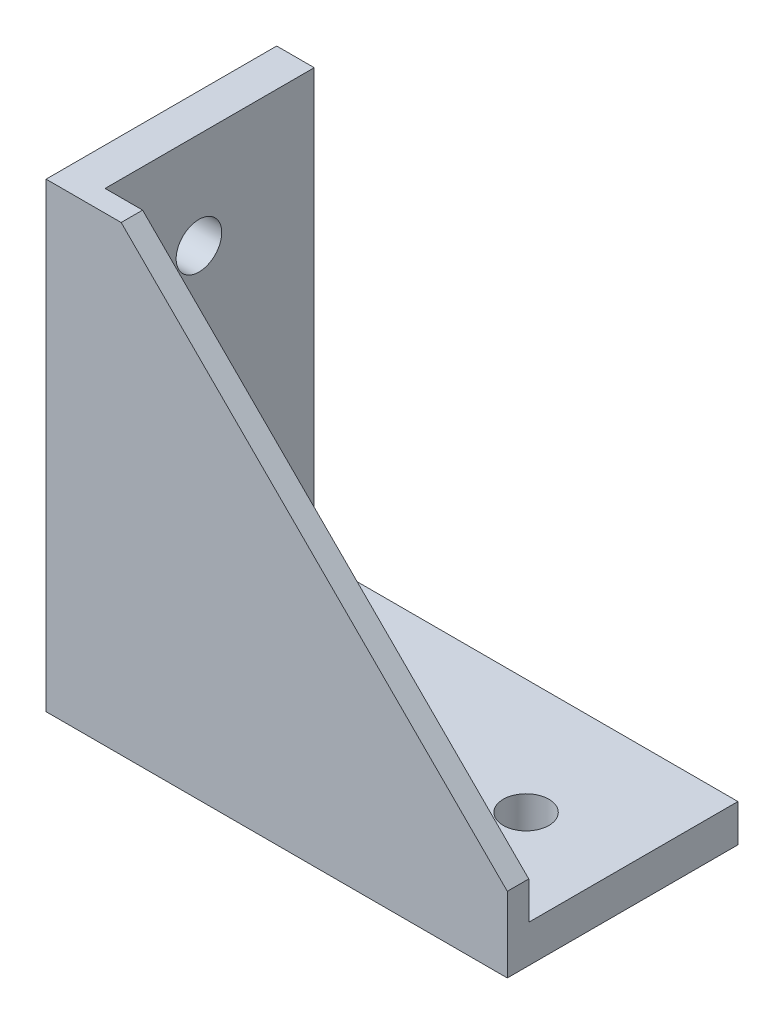
SolidWorks part; units mm, degrees
material "Алюминиевый сплав"
ref_plane "Спереди" through (0, 0, 0) normal (0, 0, 1) x (1, 0, 0)
ref_plane "Сверху" through (0, 0, 0) normal (0, 1, 0) x (1, 0, 0)
ref_plane "Справа" through (0, 0, 0) normal (1, 0, 0) x (0, 0, -1)
sketch "Эскиз1" plane through (0, 0, 0) normal (0, 0, 1) x (1, 0, 0)
  line L0 (0, 86) -> (0, 0)
  line L1 (0, 0) -> (86, 0)
  line L2 (86, 0) -> (86, 7)
  line L4 (7, 86) -> (0, 86)
  line L5 (7, 86) -> (7, 7)
  line L6 (7, 7) -> (86, 7)
  dimension "D1" = 86
  dimension "D2" = 7
extrude "Бобышка-Вытянуть1" add sketch "Эскиз1" along normal mid plane 43
sketch "Эскиз2" plane through (0, 0, 21.5) normal (0, 0, 1) x (1, 0, 0)
  line L1 (86, 7) -> (7, 7)
  line L2 (7, 7) -> (7, 86)
  line L3 (86, 0) -> (86, 7) construction
  line L4 (7, 86) -> (14, 86)
  line L5 (14, 86) -> (86, 14)
  line L6 (86, 14) -> (86, 7)
extrude "Бобышка-Вытянуть2" add sketch "Эскиз2" against normal blind 4
sketch "Эскиз3" plane through (0, 7, 0) normal (0, 1, 0) x (1, 0, 0)
  line L0 (20, 0) -> (46, 0) construction
  line L1 (20, 4.25) -> (46, 4.25)
  line L2 (20, -4.25) -> (46, -4.25)
  line L3 (0, -21.5) -> (0, 21.5) construction
  arc A0 (20, 4.25) -> (20, -4.25) centre (20, 0) ccw
  arc A1 (46, -4.25) -> (46, 4.25) centre (46, 0) ccw
  circle A2 centre (68, 0) radius 4.25
  point P2 (33, 0)
  dimension "D2" = 8.5
  dimension "D3" = 20
  dimension "D4" = 22
  dimension "D1" = 26
extrude "Вырез-Вытянуть1" cut sketch "Эскиз3" against normal through all
sketch "Эскиз4" plane through (0, 0, 0) normal (0, -1, 0) x (1, 0, 0)
  line L0 (0, 21.5) -> (0, -21.5) construction
  line L1 (3, -5) -> (6, -5)
  line L2 (3, -5) -> (3, 5)
  line L3 (3, 5) -> (6, 5)
  line L4 (6, -5) -> (6, 5)
  line L5 (3, -5) -> (6, 5) construction
  line L6 (3, 5) -> (6, -5) construction
  line L7 (80, -5) -> (83, -5)
  line L8 (80, -5) -> (80, 5)
  line L9 (80, 5) -> (83, 5)
  line L10 (83, -5) -> (83, 5)
  line L11 (80, -5) -> (83, 5) construction
  line L12 (80, 5) -> (83, -5) construction
  line L13 (86, 21.5) -> (86, -21.5) construction
  point P0 (4.5, 0)
  point P5 (81.5, 0)
  dimension "D1" = 3
  dimension "D2" = 3
  dimension "D3" = 10
  dimension "D4" = 3
extrude "Бобышка-Вытянуть3" add sketch "Эскиз4" along normal blind 3
ref_plane "Плоскость1" through (0, 0, 0) normal (-0.7071, 0.7071, 0) x (0.7071, 0.7071, 0)
mirror "Зеркальное отражение3" about plane through (0, 0, 0) normal (-0.7071, 0.7071, 0) of "Бобышка-Вытянуть3", "Вырез-Вытянуть1"
